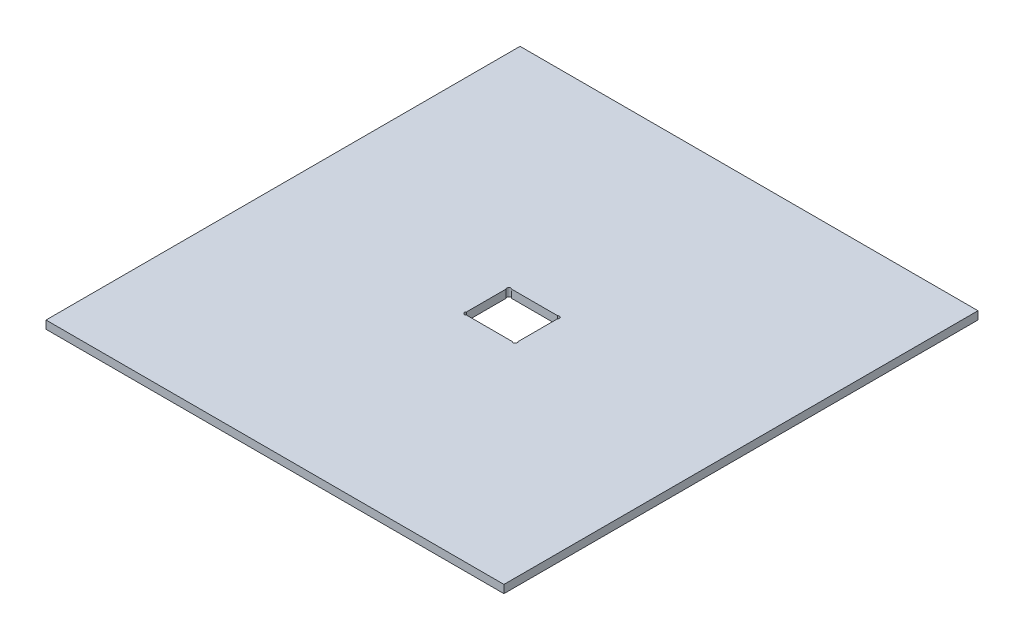
SolidWorks part; units mm, degrees
ref_plane "Front Plane" through (0, 0, 0) normal (0, 0, 1) x (1, 0, 0)
ref_plane "Top Plane" through (0, 0, 0) normal (0, 1, 0) x (1, 0, 0)
ref_plane "Right Plane" through (0, 0, 0) normal (1, 0, 0) x (0, 0, -1)
sketch "Sketch1" plane through (0, 0, 0) normal (0, 1, 0) x (1, 0, 0)
  line L4 (0, 0) -> (0, 187.325)
  line L5 (0, 187.325) -> (180.975, 187.325)
  line L6 (180.975, 187.325) -> (180.975, 0)
  line L7 (180.975, 0) -> (0, 0)
  line L8 (0, 187.325) -> (180.975, 0) construction
  dimension "D1" = 180.975
  dimension "D2" = 187.325
extrude "Boss-Extrude1" add sketch "Sketch1" along normal blind 3.175
sketch "Sketch2" plane through (0, 3.175, 0) normal (0, 1, 0) x (1, 0, 0)
  line L0 (0, 187.325) -> (180.975, 0) construction
  line L2 (80.3275, 84.7725) -> (100.6475, 84.7725)
  line L3 (80.3275, 84.7725) -> (80.3275, 102.5525)
  line L4 (80.3275, 102.5525) -> (100.6475, 102.5525)
  line L5 (100.6475, 84.7725) -> (100.6475, 102.5525)
  line L6 (80.3275, 84.7725) -> (100.6475, 102.5525) construction
  line L7 (80.3275, 102.5525) -> (100.6475, 84.7725) construction
  point P4 (90.4875, 93.6625)
  dimension "D1" = 20.32
  dimension "D2" = 17.78
extrude "Cut-Extrude1" cut sketch "Sketch2" against normal through all
sketch "Sketch3" plane through (0, 3.175, 0) normal (0, 1, 0) x (1, 0, 0)
  line L0 (80.3275, 84.7725) -> (100.6475, 84.7725) construction
  line L1 (100.6475, 84.7725) -> (100.6475, 102.5525) construction
  line L2 (100.6475, 102.5525) -> (80.3275, 102.5525) construction
  line L3 (80.3275, 102.5525) -> (80.3275, 84.7725) construction
  line L4 (80.3275, 84.7725) -> (81.45, 84.7725) construction
  line L5 (100.6475, 84.7725) -> (100.6475, 85.895) construction
  line L6 (100.6475, 102.5525) -> (99.525, 102.5525) construction
  line L7 (80.3275, 102.5525) -> (80.3275, 101.43) construction
  line L8 (80.3275, 85.895) -> (80.3275, 84.7725) construction
  line L9 (99.525, 84.7725) -> (100.6475, 84.7725) construction
  line L10 (100.6475, 101.43) -> (100.6475, 102.5525) construction
  line L11 (81.45, 102.5525) -> (80.3275, 102.5525) construction
  circle A0 centre (80.8888, 101.9912) radius 0.7937
  circle A1 centre (100.0862, 101.9912) radius 0.7937
  circle A2 centre (80.8888, 85.3338) radius 0.7937
  circle A3 centre (100.0862, 85.3338) radius 0.7937
  dimension "D1" = 1.5875
extrude "Cut-Extrude2" cut sketch "Sketch3" against normal blind 3.175
sketch "Sketch4" plane through (0, 3.175, 0) normal (0, 1, 0) x (1, 0, 0)
  line L0 (0, 0) -> (180.975, 0) construction
  line L1 (180.975, 0) -> (180.975, 187.325) construction
  line L2 (0, 187.325) -> (0, 0) construction
  line L3 (180.975, 187.325) -> (0, 187.325) construction
  line L4 (0, 0) -> (180.975, 0)
  line L5 (180.975, 0) -> (180.975, 187.325)
  line L6 (0, 187.325) -> (0, 0)
  line L7 (180.975, 187.325) -> (0, 187.325)
  line L8 (0.1016, 0.1016) -> (180.8734, 0.1016)
  line L9 (180.8734, 0.1016) -> (180.8734, 187.2234)
  line L10 (180.8734, 187.2234) -> (0.1016, 187.2234)
  line L11 (0.1016, 187.2234) -> (0.1016, 0.1016)
  dimension "D1" = 0.1016
extrude "Cut-Extrude3" cut sketch "Sketch4" against normal blind 3.175
